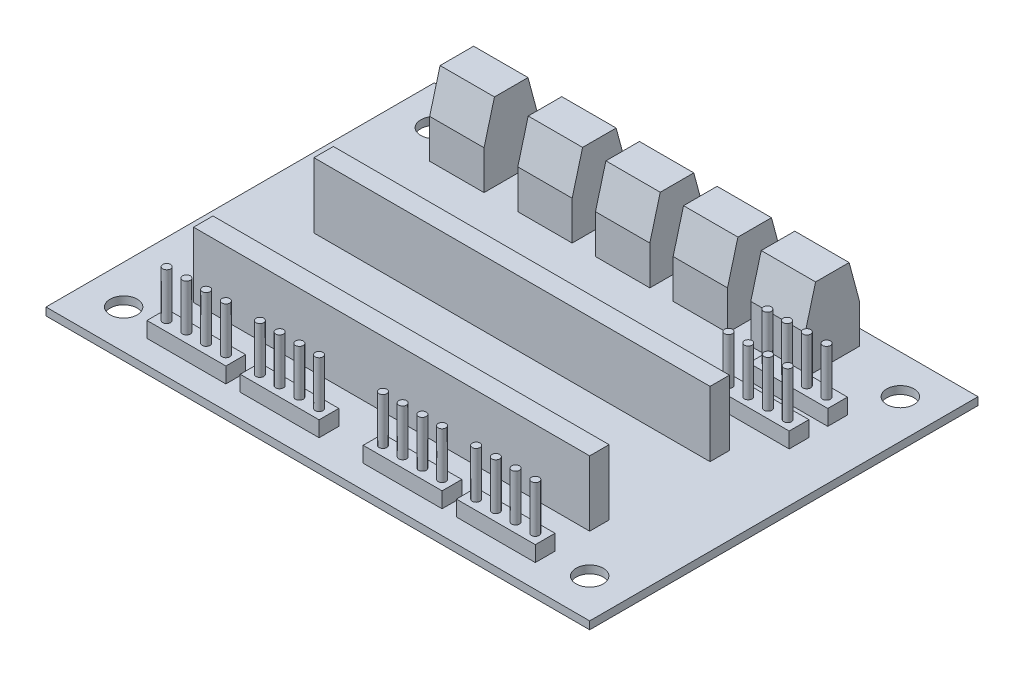
SolidWorks part; units mm, degrees
material "ABS"
ref_plane "Спереди" through (0, 0, 0) normal (0, 0, 1) x (1, 0, 0)
ref_plane "Сверху" through (0, 0, 0) normal (0, 1, 0) x (1, 0, 0)
ref_plane "Справа" through (0, 0, 0) normal (1, 0, 0) x (0, 0, -1)
sketch "Эскиз2" plane through (0, 0, 0) normal (0, 1, 0) x (1, 0, 0)
  line L0 (0, 25) -> (113.3637, 25) construction
  line L1 (0, 0) -> (70, 0)
  line L2 (0, 0) -> (0, 50)
  line L3 (0, 50) -> (70, 50)
  line L4 (70, 0) -> (70, 50)
  line L5 (35, 50) -> (35, -7.1391) construction
  circle A0 centre (5, 45) radius 1.75
  circle A1 centre (65, 45) radius 1.75
  circle A2 centre (65, 5) radius 1.75
  circle A3 centre (5, 5) radius 1.75
  dimension "D3" = 3.5
  dimension "D1" = 70
  dimension "D2" = 50
  dimension "D4" = 5
  dimension "D5" = 5
extrude "Бобышка-Вытянуть1" add sketch "Эскиз2" along normal blind 1
sketch "Эскиз3" plane through (0, 1, 0) normal (0, 1, 0) x (1, 0, 0)
  line L0 (0, 0) -> (70, 0) construction
  line L1 (9, 12.5) -> (60, 12.5)
  line L2 (9, 12.5) -> (9, 10)
  line L3 (9, 10) -> (60, 10)
  line L4 (60, 12.5) -> (60, 10)
  line L9 (70, 0) -> (70, 50) construction
  line L10 (60, 12.5) -> (60, 19) construction
  line L11 (60, 19) -> (7.0253, 19) construction
  line L12 (9, 28) -> (60, 28)
  line L13 (60, 25.5) -> (60, 28)
  line L14 (9, 25.5) -> (60, 25.5)
  line L15 (9, 25.5) -> (9, 28)
  dimension "D1" = 2.5
  dimension "D2" = 51
  dimension "D6" = 10
  dimension "D7" = 10
extrude "Бобышка-Вытянуть2" add sketch "Эскиз3" along normal blind 8.4
sketch "Эскиз4" plane through (0, 1, 0) normal (0, 1, 0) x (1, 0, 0)
  line L0 (70, 0) -> (70, 50) construction
  line L1 (60, 5.54) -> (49.84, 5.54)
  line L2 (60, 5.54) -> (60, 3)
  line L3 (60, 3) -> (49.84, 3)
  line L4 (49.84, 5.54) -> (49.84, 3)
  line L5 (0, 0) -> (70, 0) construction
  line L6 (48, 5.54) -> (48, 3)
  line L7 (35, 0) -> (35, 38.4524) construction
  line L8 (48, 5.54) -> (37.84, 5.54)
  line L9 (37.84, 5.54) -> (37.84, 3)
  line L10 (48, 3) -> (37.84, 3)
  line L11 (10, 3) -> (20.16, 3)
  line L12 (20.16, 5.54) -> (20.16, 3)
  line L13 (10, 5.54) -> (20.16, 5.54)
  line L14 (10, 5.54) -> (10, 3)
  line L15 (22, 5.54) -> (32.16, 5.54)
  line L16 (32.16, 5.54) -> (32.16, 3)
  line L17 (22, 3) -> (32.16, 3)
  line L18 (22, 5.54) -> (22, 3)
  line L19 (53.4823, 37.0132) -> (63.6423, 37.0132)
  line L20 (53.4823, 37.0132) -> (53.4823, 39.5532)
  line L21 (53.4823, 39.5532) -> (63.6423, 39.5532)
  line L22 (63.6423, 37.0132) -> (63.6423, 39.5532)
  line L23 (53.5146, 32.0132) -> (63.6746, 32.0132)
  line L24 (53.5146, 32.0132) -> (53.5146, 34.5532)
  line L25 (53.5146, 34.5532) -> (63.6746, 34.5532)
  line L26 (63.6746, 32.0132) -> (63.6746, 34.5532)
  dimension "D1" = 2.54
  dimension "D2" = 10.16
  dimension "D3" = 10
  dimension "D4" = 3
  dimension "D6" = 5
  dimension "D5" = 2
extrude "Бобышка-Вытянуть3" add sketch "Эскиз4" along normal blind 2
sketch "Эскиз5" plane through (0, 3, 0) normal (0, 1, 0) x (1, 0, 0)
  line L0 (60, 3) -> (60, 5.54) construction
  line L1 (49.84, 3) -> (60, 3) construction
  line L2 (35, 0) -> (35, 20.127) construction
  line L3 (0, 0) -> (70, 0) construction
  circle A0 centre (58.73, 4.27) radius 0.5
  circle A1 centre (56.19, 4.27) radius 0.5
  circle A2 centre (53.65, 4.27) radius 0.5
  circle A3 centre (51.11, 4.27) radius 0.5
  circle A4 centre (46.73, 4.27) radius 0.5
  circle A5 centre (44.19, 4.27) radius 0.5
  circle A6 centre (41.65, 4.27) radius 0.5
  circle A7 centre (39.11, 4.27) radius 0.5
  circle A8 centre (25.81, 4.27) radius 0.5
  circle A9 centre (11.27, 4.27) radius 0.5
  circle A10 centre (13.81, 4.27) radius 0.5
  circle A11 centre (16.35, 4.27) radius 0.5
  circle A12 centre (18.89, 4.27) radius 0.5
  circle A13 centre (23.27, 4.27) radius 0.5
  circle A14 centre (28.35, 4.27) radius 0.5
  circle A15 centre (30.89, 4.27) radius 0.5
  circle A16 centre (54.671, 33.2084) radius 0.5
  circle A17 centre (54.671, 38.2084) radius 0.5
  circle A20 centre (57.211, 33.2084) radius 0.5
  circle A21 centre (59.751, 33.2084) radius 0.5
  circle A22 centre (62.291, 33.2084) radius 0.5
  circle A23 centre (57.211, 38.2084) radius 0.5
  circle A24 centre (59.751, 38.2084) radius 0.5
  circle A25 centre (62.291, 38.2084) radius 0.5
  dimension "D1" = 1
  dimension "D2" = 1.27
  dimension "D3" = 1.27
  dimension "D4" = 4
  dimension "D5" = 2
  dimension "D6" = 4
  dimension "D7" = 2
extrude "Бобышка-Вытянуть4" add sketch "Эскиз5" along normal blind 6
sketch "Эскиз6" plane through (0, 1, 0) normal (0, 1, 0) x (1, 0, 0)
  line L0 (19.7472, 48.0002) -> (26.7472, 48.0002)
  line L5 (8.4463, 40.9536) -> (8.4463, 47.9536)
  line L6 (8.4463, 40.9536) -> (15.4463, 40.9536)
  line L7 (15.4463, 40.9536) -> (15.4463, 47.9536)
  line L8 (8.4463, 47.9536) -> (15.4463, 47.9536)
  line L9 (19.7472, 48.0002) -> (19.7472, 41.0002)
  line L10 (19.7472, 41.0002) -> (26.7472, 41.0002)
  line L11 (26.7472, 48.0002) -> (26.7472, 41.0002)
  line L12 (29.7472, 48.0002) -> (36.7472, 48.0002)
  line L13 (36.7472, 48.0002) -> (36.7472, 41.0002)
  line L14 (29.7472, 41.0002) -> (36.7472, 41.0002)
  line L15 (29.7472, 48.0002) -> (29.7472, 41.0002)
  line L16 (39.7472, 48.0002) -> (46.7472, 48.0002)
  line L17 (46.7472, 48.0002) -> (46.7472, 41.0002)
  line L18 (39.7472, 41.0002) -> (46.7472, 41.0002)
  line L19 (39.7472, 48.0002) -> (39.7472, 41.0002)
  line L20 (49.7472, 48.0002) -> (56.7472, 48.0002)
  line L21 (56.7472, 48.0002) -> (56.7472, 41.0002)
  line L22 (49.7472, 41.0002) -> (56.7472, 41.0002)
  line L23 (49.7472, 48.0002) -> (49.7472, 41.0002)
  dimension "D1" = 7
  dimension "D2" = 7
  dimension "D3" = 4
extrude "Бобышка-Вытянуть5" add sketch "Эскиз6" along normal blind 10
chamfer "Фаска1" distance 5 angle 15 10 edges at (53.2472, 11, -48.0002) (53.2472, 11, -41.0002) (43.2472, 11, -48.0002) (43.2472, 11, -41.0002) (33.2472, 11, -41.0002) (33.2472, 11, -48.0002) (23.2472, 11, -48.0002) (23.2472, 11, -41.0002) (11.9463, 11, -47.9536) (11.9463, 11, -40.9536)
sketch "Эскиз7" plane through (0, 0, -47.9536) normal (0, 0, -1) x (-1, 0, 0)
  circle A0 centre (-10.2599, 3.2184) radius 1
  circle A1 centre (-13.2812, 3.2184) radius 1
  circle A2 centre (-21.7063, 3.2233) radius 1
  circle A3 centre (-24.7277, 3.2233) radius 1
  circle A4 centre (-34.7277, 3.2233) radius 1
  circle A5 centre (-31.7063, 3.2233) radius 1
  circle A6 centre (-44.7277, 3.2233) radius 1
  circle A7 centre (-41.7063, 3.2233) radius 1
  circle A8 centre (-54.7277, 3.2233) radius 1
  circle A9 centre (-51.7063, 3.2233) radius 1
  dimension "D1" = 4
extrude "Вырез-Вытянуть1" cut sketch "Эскиз7" against normal blind 2 from surface at 0.0466 starting at face at (33.2472, 3.5, -48.0002)
